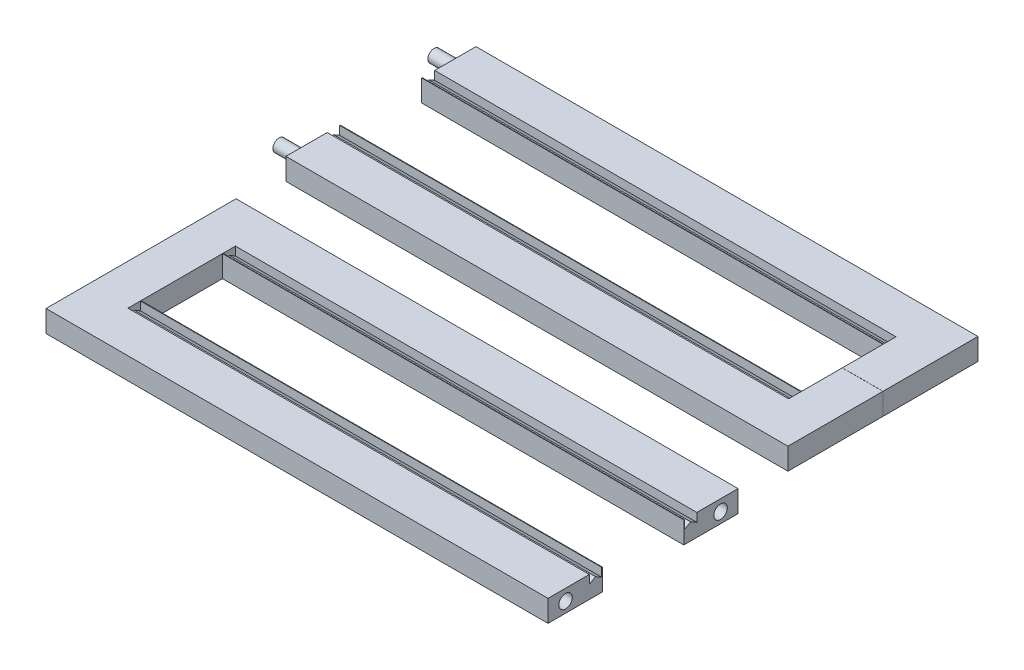
SolidWorks part; units mm, degrees
ref_plane "Front Plane" through (0, 0, 0) normal (0, 0, 1) x (1, 0, 0)
ref_plane "Top Plane" through (0, 0, 0) normal (0, 1, 0) x (1, 0, 0)
ref_plane "Right Plane" through (0, 0, 0) normal (1, 0, 0) x (0, 0, -1)
sketch "Sketch1" plane through (0, 0, 0) normal (0, 1, 0) x (1, 0, 0)
  line L0 (-199.8762, 57.4725) -> (-199.8762, 13.0225) construction
  line L1 (-434.8262, 57.4725) -> (35.0738, 57.4725)
  line L2 (16.038, 13.0225) -> (16.038, 32.0725)
  line L3 (16.038, 32.0725) -> (-415.7904, 32.0725)
  line L4 (35.0738, 57.4725) -> (35.0738, 13.0225)
  line L5 (-415.7904, 13.0225) -> (-415.7904, 32.0725)
  line L6 (-199.8762, 13.0225) -> (35.0738, 57.4725) construction
  line L7 (-434.8262, 57.4725) -> (-434.8262, 13.0225)
  line L8 (32.2526, 13.0225) -> (-199.8762, 13.0225) construction
  line L9 (-434.8262, 13.0225) -> (-415.7904, 13.0225)
  line L10 (16.038, 13.0225) -> (35.0738, 13.0225)
  line L11 (16.038, 13.0225) -> (-415.7904, 13.0225)
  line L12 (16.038, 32.0725) -> (16.038, 57.4725)
  point P0 (-199.8762, 13.0225)
  point P14 (-199.8762, 32.0725)
  dimension "D1" = 19.05
extrude "Boss-Extrude1" add sketch "Sketch1" along normal blind 10.16 contours L3 L12 L1 L7 L9 L5 | L12 L2 L10 L4 L1
sketch "Sketch2" plane through (0, 10.16, 0) normal (0, 1, 0) x (1, 0, 0)
  line L0 (15.3645, 14.5465) -> (15.3645, 57.4725)
  line L1 (-434.8262, 57.4725) -> (35.0738, 57.4725) construction
  line L2 (16.038, 13.0225) -> (16.038, 32.0725) construction
  line L3 (16.038, 13.0225) -> (16.038, 32.0725)
  line L4 (-434.8262, 57.4725) -> (35.0738, 57.4725)
  line L5 (16.038, 32.0725) -> (16.038, 57.4725)
  line L6 (35.0738, 57.4725) -> (35.0738, 13.0225) construction
  line L7 (35.0738, 57.4725) -> (35.0738, 13.0225)
sketch "Sketch3" plane through (35.0738, 0, 0) normal (1, 0, 0) x (0, 0, -1)
  line L0 (57.4725, 10.16) -> (13.0225, 10.16) construction
  line L1 (57.4725, 10.16) -> (13.0225, 10.16)
  line L4 (32.3389, 10.16) -> (32.3389, 6.1527)
  line L5 (35.2475, 7.8319) -> (32.3389, 6.1527)
  line L6 (35.2475, 7.8319) -> (38.156, 6.1527)
  line L7 (38.156, 10.16) -> (38.156, 6.1527)
  line L8 (32.3389, 10.16) -> (38.156, 10.16)
extrude "Cut-Extrude1" cut sketch "Sketch3" against normal blind 469.9 contours L7 L1 L4 L5 L6
sketch "Sketch7" plane through (35.0738, 0, 0) normal (1, 0, 0) x (0, 0, -1)
  line L0 (28.3559, 10.16) -> (28.3559, 4.4679)
  line L1 (28.3559, 10.16) -> (40.7589, 10.16)
  line L2 (28.3559, 4.4679) -> (40.7589, 4.4679)
  line L3 (40.7589, 10.16) -> (40.7589, 4.4679)
  line L4 (57.4725, 10.16) -> (13.0225, 10.16) construction
extrude "Boss-Extrude2" add sketch "Sketch7" against normal blind 19.05
sketch "Sketch8" plane through (-434.8262, 0, 0) normal (-1, 0, 0) x (0, 0, 1)
  line L0 (-57.4725, 10.16) -> (-57.4725, 0)
  line L1 (-57.4725, 10.16) -> (-12.9988, 10.16)
  line L2 (-57.4725, 0) -> (-12.9988, 0)
  line L3 (-12.9988, 10.16) -> (-12.9988, 0)
extrude "Boss-Extrude3" add sketch "Sketch8" against normal blind 19.05
ref_plane "Plane3" through (0, 0, -13.0106) normal (0, 0, 1) x (1, 0, 0)
sketch "Sketch9" plane through (0, 0, -13.0106) normal (0, 0, 1) x (1, 0, 0)
  line L0 (-430.6828, 6.1804) -> (95.5684, 6.1804) construction
mirror "Mirror1" about plane through (-415.7762, 10.16, -12.9988) normal (0, 0, 1) of bodies 105
sketch "Sketch11" plane through (0, 0, 0) normal (0, -1, 0) x (1, 0, 0)
  line L0 (-425.1563, 31.4749) -> (-425.1563, -53.6177) construction
  line L1 (-434.8262, 31.4749) -> (35.0738, 31.4749) construction
  line L2 (-199.8762, 31.4749) -> (-199.8762, -116.9894) construction
  line L3 (16.038, 6.0749) -> (-415.7762, 6.0749) construction
  line L4 (16.038, 6.0749) -> (-415.7762, 6.0749)
  line L5 (-430.6828, -13.0106) -> (95.5684, -13.0106) construction
  line L6 (-430.6828, -13.0106) -> (95.5684, -13.0106)
  circle A0 centre (-425.1563, 10.2268) radius 5.7912
  circle A1 centre (-425.1563, -36.248) radius 5.7912
  circle A2 centre (25.4039, -36.248) radius 5.7912
  circle A3 centre (25.4039, 10.2268) radius 5.7912
extrude "Cut-Extrude2" cut sketch "Sketch11" against normal blind 3.81 contours A0 | A2 | A3 | A1
sketch "Sketch12" plane through (0, 0, 31.4749) normal (0, 0, 1) x (1, 0, 0)
  line L5 (-199.8762, -28.6923) -> (-199.8762, 81.4582)
surface "Surface-Extrude1" sketch "Sketch12" parameters "D1"=127
split "Split1" trimming surface bodies 108 bodies to split 107 resulting bodies 109 110 111
move or copy body "Body-Move/Copy1" bodies to move or copy 109 copy no translate (240.4766, 0, 117.8098)
sketch "Sketch13" plane through (40.6005, 0, 0) normal (1, 0, 0) x (0, 0, -1)
  circle A0 centre (-68.5495, 4.9038) radius 3.1585
extrude "Cut-Extrude3" cut sketch "Sketch13" against normal blind 12.7
sketch "Sketch15" plane through (-199.8762, 0, 0) normal (-1, 0, 0) x (0, 0, 1)
  circle A0 centre (-49.2603, 4.9038) radius 2.9103
extrude "Boss-Extrude6" add sketch "Sketch15" along normal blind 11.43
sketch "Sketch16" plane through (-199.8762, 0, 0) normal (-1, 0, 0) x (0, 0, 1)
  line L0 (27.9214, 0) -> (27.9214, 4.9038)
  line L1 (6.0749, 0) -> (31.4749, 0) construction
  line L2 (31.4749, 4.9038) -> (23.2627, 4.9038)
  line L3 (31.4749, 10.16) -> (31.4749, 0) construction
  circle A0 centre (23.2627, 4.9038) radius 2.9157
extrude "Boss-Extrude7" add sketch "Sketch16" along normal blind 11.43
sketch "Sketch17" plane through (40.6005, 0, 0) normal (1, 0, 0) x (0, 0, -1)
  line L0 (-145.6913, 0) -> (-145.6913, 4.9038)
  line L1 (-123.8846, 0) -> (-149.2846, 0) construction
  line L2 (-149.2846, 4.9038) -> (-141.0725, 4.9038)
  line L3 (-149.2846, 10.16) -> (-149.2846, 0) construction
  circle A0 centre (-141.0725, 4.9038) radius 3.1391
extrude "Cut-Extrude4" cut sketch "Sketch17" against normal blind 12.7
